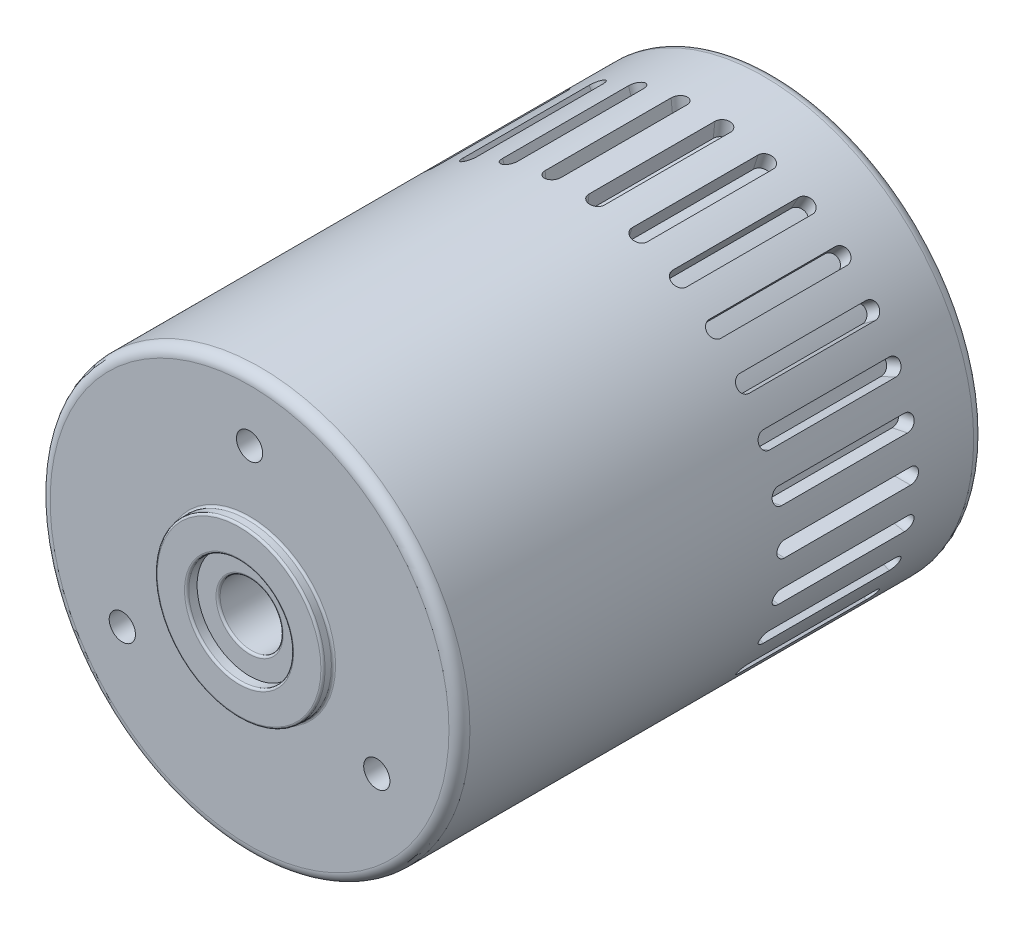
SolidWorks part; units mm, degrees
ref_plane "Front Plane" through (0, 0, 0) normal (0, 0, 1) x (1, 0, 0)
ref_plane "Top Plane" through (0, 0, 0) normal (0, 1, 0) x (1, 0, 0)
ref_plane "Right Plane" through (0, 0, 0) normal (1, 0, 0) x (0, 0, -1)
sketch "Sketch1" plane through (0, 0, 0) normal (0, 0, 1) x (1, 0, 0)
  circle A0 centre (0, 0) radius 10
  circle A1 centre (0, 0) radius 1.5 construction
  circle A2 centre (0, 0) radius 2.5 construction
  circle A3 centre (0, 0) radius 4 construction
  dimension "D1" = 20
  dimension "D2" = 3
  dimension "D3" = 5
  dimension "D4" = 8
extrude "Boss-Extrude1" add sketch "Sketch1" against normal blind 25
sketch "Sketch2" plane through (0, 0, 0) normal (0, 0, 1) x (1, 0, 0)
  circle A0 centre (0, 0) radius 4 construction
  circle A1 centre (0, 0) radius 2.5 construction
  circle A2 centre (0, 0) radius 4
  circle A3 centre (0, 0) radius 2.5
extrude "Boss-Extrude2" add sketch "Sketch2" along normal blind 0.5
sketch "Sketch3" plane through (0, 0, -25) normal (0, 0, -1) x (-1, 0, 0)
  circle A0 centre (0, 0) radius 1.5
  dimension "D1" = 3
extrude "Boss-Extrude3" add sketch "Sketch3" along normal blind 0.5
sketch "Sketch4" plane through (0, 0, 0) normal (1, 0, 0) x (0, 0, -1)
  line L0 (0, 0) -> (35.6396, 0) construction
  line L1 (15.5, 0) -> (21.5, 0) construction
  line L2 (15.5, 0.375) -> (21.5, 0.375)
  line L3 (15.5, -0.375) -> (21.5, -0.375)
  line L4 (0, 10) -> (0, -10) construction
  arc A0 (15.5, 0.375) -> (15.5, -0.375) centre (15.5, 0) ccw
  arc A1 (21.5, -0.375) -> (21.5, 0.375) centre (21.5, 0) ccw
  point P5 (18.5, 0)
  dimension "D1" = 6
  dimension "D2" = 18.5
  dimension "D3" = 0.75
extrude "Cut-Extrude1" cut sketch "Sketch4" against normal offset from surface (20.757 mm away) 0.75 from offset 30
pattern_circular "CirPattern1" count 30 over 360 about axis through (0, 0, 0) along (0, 0, 1) of "Cut-Extrude1"
sketch "Sketch5" plane through (0, 0, 0) normal (0, 0, 1) x (1, 0, 0)
  circle A0 centre (0, 0) radius 1.5 construction
  circle A1 centre (0, 0) radius 1.5
extrude "Cut-Extrude2" cut sketch "Sketch5" against normal blind 5
fillet "Fillet1" radius 0.5 2 edges at (10, 0, -25) (10, 0, 0)
sketch "Sketch6" plane through (0, 0, 0) normal (0, 0, 1) x (1, 0, 0)
  circle A0 centre (0, 0) radius 7 construction
  circle A1 centre (0, 7) radius 0.625
  circle A2 centre (6.0622, -3.5) radius 0.625
  circle A3 centre (-6.0622, -3.5) radius 0.625
  point P12 (0, 0)
  dimension "D1" = 14
  dimension "D2" = 1.25
  dimension "D3" = 3
extrude "Cut-Extrude3" cut sketch "Sketch6" against normal blind 5
fillet "Fillet2" radius 0.1 6 edges at (4, 0, 0) (4, 0, 0.5) (-1.5, 0, -25) (-1.5, 0, -25.5) (1.5, 0, 0) (2.5, 0, 0.5)
